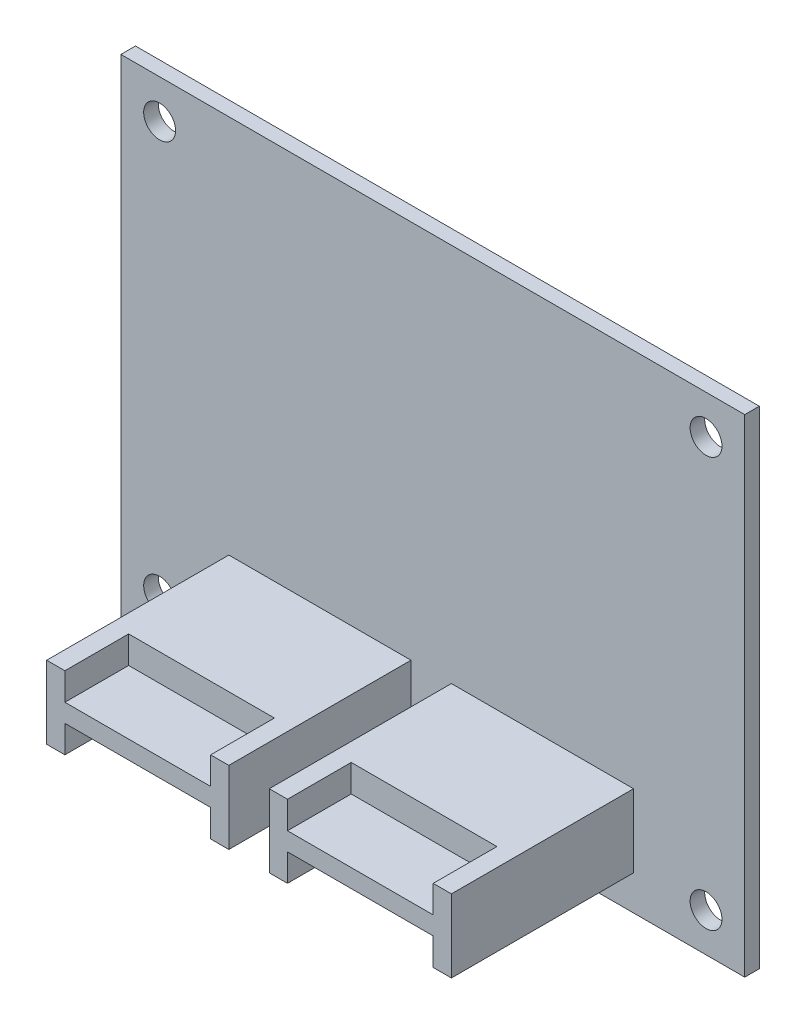
SolidWorks part; units mm, degrees
ref_plane "Front Plane" through (0, 0, 0) normal (0, 0, 1) x (1, 0, 0)
ref_plane "Top Plane" through (0, 0, 0) normal (0, 1, 0) x (1, 0, 0)
ref_plane "Right Plane" through (0, 0, 0) normal (1, 0, 0) x (0, 0, -1)
sketch "Sketch1" plane through (0, 0, 0) normal (0, 0, 1) x (1, 0, 0)
  line L0 (-34.25, -26.75) -> (34.25, 26.75) construction
  line L1 (-34.25, 26.75) -> (34.25, 26.75)
  line L2 (-34.25, 26.75) -> (-34.25, -26.75)
  line L3 (-34.25, -26.75) -> (34.25, -26.75)
  line L4 (34.25, 26.75) -> (34.25, -26.75)
  line L5 (0, 0) -> (0, 57.493) construction
  line L6 (0, 0) -> (67.7037, 0) construction
  circle A0 centre (-30, 22.5) radius 1.75
  circle A1 centre (30, 22.5) radius 1.75
  circle A2 centre (-30, -22.5) radius 1.75
  circle A3 centre (30, -22.5) radius 1.75
  point P4 (0, 0)
  point P16 (-30.0059, 24.3565)
  point P18 (19.65, 22.6302)
  point P19 (-27.2642, 8.9215)
  point P20 (24.8289, 12.5772)
  point P21 (0, 0)
  point P22 (28.1068, 5.157)
  point P23 (30.924, -7.0757)
  point P24 (0, 0)
  point P25 (0, 0)
  dimension "D3" = 3.5
  dimension "D1" = 68.5
  dimension "D2" = 53.5
  dimension "D4" = 60
  dimension "D5" = 45
extrude "Boss-Extrude1" add sketch "Sketch1" along normal mid plane 1.6
sketch "Sketch2" plane through (0, 0, 0.8) normal (0, 0, 1) x (1, 0, 0)
  line L1 (-22.3994, -14.931) -> (-2.3994, -14.931)
  line L2 (-22.3994, -14.931) -> (-22.3994, -22.931)
  line L3 (-22.3994, -22.931) -> (-2.3994, -22.931)
  line L4 (-2.3994, -14.931) -> (-2.3994, -22.931)
  line L5 (2.0398, -14.931) -> (22.0398, -14.931)
  line L6 (2.0398, -14.931) -> (2.0398, -22.931)
  line L7 (2.0398, -22.931) -> (22.0398, -22.931)
  line L8 (22.0398, -14.931) -> (22.0398, -22.931)
  point P8 (-19.2807, -21.859)
  point P9 (-22.3994, -22.1882)
  point P10 (21.9477, -20.2568)
  point P11 (2.0398, -22.931)
  dimension "D1" = 20
  dimension "D2" = 8
extrude "Boss-Extrude2" add sketch "Sketch2" along normal blind 20
sketch "Sketch3" plane through (0, 0, 20.8) normal (0, 0, 1) x (1, 0, 0)
  line L14 (-2.3994, -14.931) -> (-22.3994, -14.931) construction
  line L15 (-20.3994, -14.931) -> (-4.3994, -14.931)
  line L16 (-20.3994, -14.931) -> (-20.3994, -17.931)
  line L17 (-20.3994, -17.931) -> (-4.3994, -17.931)
  line L18 (-4.3994, -14.931) -> (-4.3994, -17.931)
  line L19 (-22.3994, -22.931) -> (-2.3994, -22.931) construction
  line L20 (-20.3994, -22.931) -> (-4.3994, -22.931)
  line L21 (-20.3994, -22.931) -> (-20.3994, -19.931)
  line L22 (-20.3994, -19.931) -> (-4.3994, -19.931)
  line L23 (-4.3994, -22.931) -> (-4.3994, -19.931)
  line L24 (22.0398, -14.931) -> (2.0398, -14.931) construction
  line L25 (4.0398, -14.931) -> (20.0398, -14.931)
  line L26 (4.0398, -14.931) -> (4.0398, -17.931)
  line L27 (4.0398, -17.931) -> (20.0398, -17.931)
  line L28 (20.0398, -14.931) -> (20.0398, -17.931)
  line L29 (2.0398, -22.931) -> (22.0398, -22.931) construction
  line L30 (4.0398, -22.931) -> (20.0398, -22.931)
  line L31 (4.0398, -22.931) -> (4.0398, -19.931)
  line L32 (4.0398, -19.931) -> (20.0398, -19.931)
  line L33 (20.0398, -22.931) -> (20.0398, -19.931)
  line L34 (-22.3994, -14.931) -> (-22.3994, -22.931) construction
  line L35 (22.0398, -22.931) -> (22.0398, -14.931) construction
  point P30 (-13.1731, -17.8169)
  dimension "D1" = 16
  dimension "D2" = 2
  dimension "D3" = 2
  dimension "D4" = 3
extrude "Cut-Extrude1" cut sketch "Sketch3" against normal blind 7
